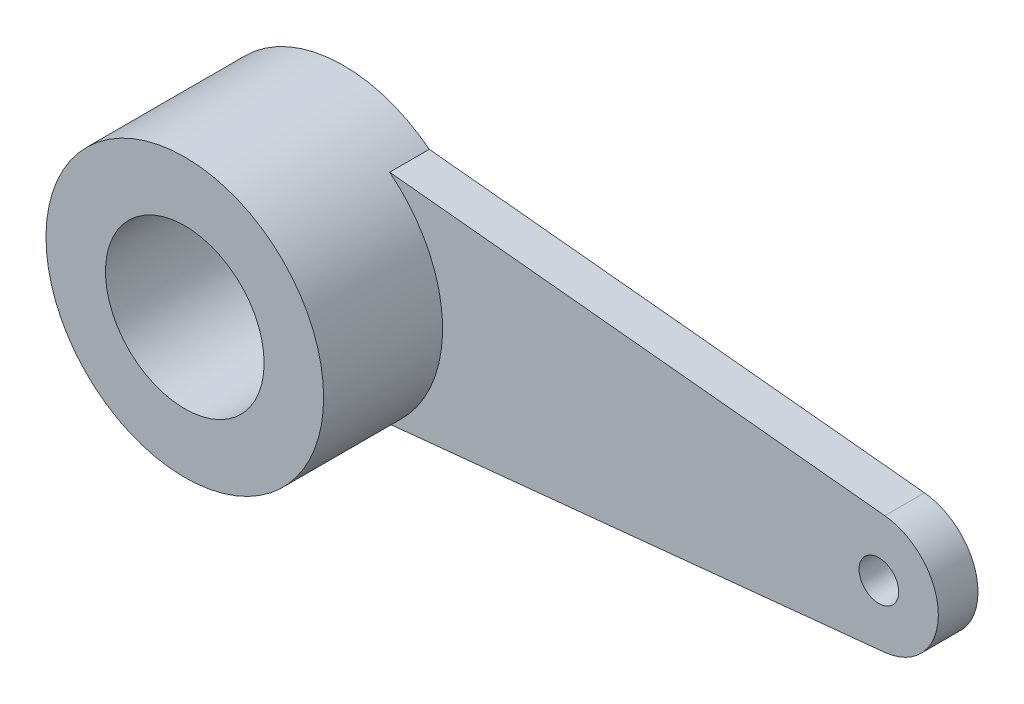
SolidWorks part; units mm, degrees
ref_plane "前视基准面" through (0, 0, 0) normal (0, 0, 1) x (1, 0, 0)
ref_plane "上视基准面" through (0, 0, 0) normal (0, 1, 0) x (1, 0, 0)
ref_plane "右视基准面" through (0, 0, 0) normal (1, 0, 0) x (0, 0, -1)
sketch "草图1" plane through (0, 0, 0) normal (0, 0, 1) x (1, 0, 0)
  line L0 (0, 0) -> (14.5, 0) construction
  line L1 (2.1651, 2.75) -> (14.6503, 1.4924)
  line L2 (2.1651, -2.75) -> (14.6503, -1.4924)
  circle A0 centre (14.5, 0) radius 1.5
  circle A1 centre (0, 0) radius 3.5
  circle A2 centre (0, 0) radius 2
  circle A3 centre (14.5, 0) radius 0.5
  dimension "D2" = 3
  dimension "D3" = 7
  dimension "D4" = 4
  dimension "D6" = 1
  dimension "D1" = 14.5
  dimension "D5" = 2.75
extrude "凸台-拉伸2" add sketch "草图1" along normal blind 1
sketch "草图2" plane through (0, 0, 1) normal (0, 0, 1) x (1, 0, 0)
  circle A0 centre (0, 0) radius 2
  circle A1 centre (0, 0) radius 3.5
  circle A2 centre (0, 0) radius 2 construction
  arc A3 (2.1651, 2.75) -> (2.1651, -2.75) centre (0, 0) ccw construction
extrude "凸台-拉伸3" add sketch "草图2" along normal blind 3
